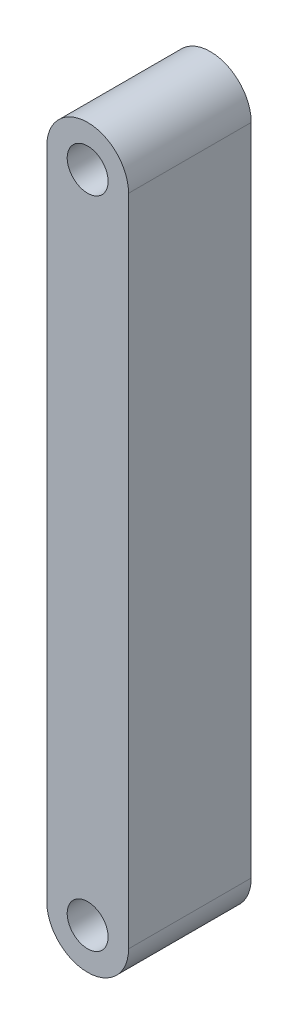
SolidWorks part; units mm, degrees
ref_plane "Front Plane" through (0, 0, 0) normal (0, 0, 1) x (1, 0, 0)
ref_plane "Top Plane" through (0, 0, 0) normal (0, 1, 0) x (1, 0, 0)
ref_plane "Right Plane" through (0, 0, 0) normal (1, 0, 0) x (0, 0, -1)
sketch "Sketch1" plane through (0, 0, 0) normal (0, 0, 1) x (1, 0, 0)
  line L1 (-5, 40) -> (5, 40)
  line L2 (-5, 40) -> (-5, -40)
  line L3 (-5, -40) -> (5, -40)
  line L4 (5, 40) -> (5, -40)
  line L5 (-5, 40) -> (5, -40) construction
  line L6 (-5, -40) -> (5, 40) construction
  circle A1 centre (0, -40) radius 5
  circle A2 centre (0, 40) radius 5
  point P0 (0, 0)
  dimension "D1" = 10
  dimension "D2" = 80
extrude "Boss-Extrude1" add sketch "Sketch1" along normal blind 15 contours A2 L2 A1 L4 | L1 A2 | L3 A1 | L1 A2 | L3 A1
sketch "Sketch2" plane through (0, 0, 15) normal (0, 0, 1) x (1, 0, 0)
  line L0 (-5, 40) -> (-5, -40) construction
  circle A0 centre (0, 40) radius 2.5
  circle A1 centre (0, -40) radius 2.5
  arc A2 (5, 40) -> (-5, 40) centre (0, 40) ccw construction
  arc A3 (-5, -40) -> (5, -40) centre (0, -40) ccw construction
  point P9 (0, 45)
  point P13 (0, -45)
  dimension "D1" = 5
  dimension "D2" = 80
  dimension "D3" = 5
  dimension "D4" = 5
  dimension "D5" = 5
extrude "Cut-Extrude1" cut sketch "Sketch2" against normal up to surface (15 mm away) up to face at (0, 0, 0)
